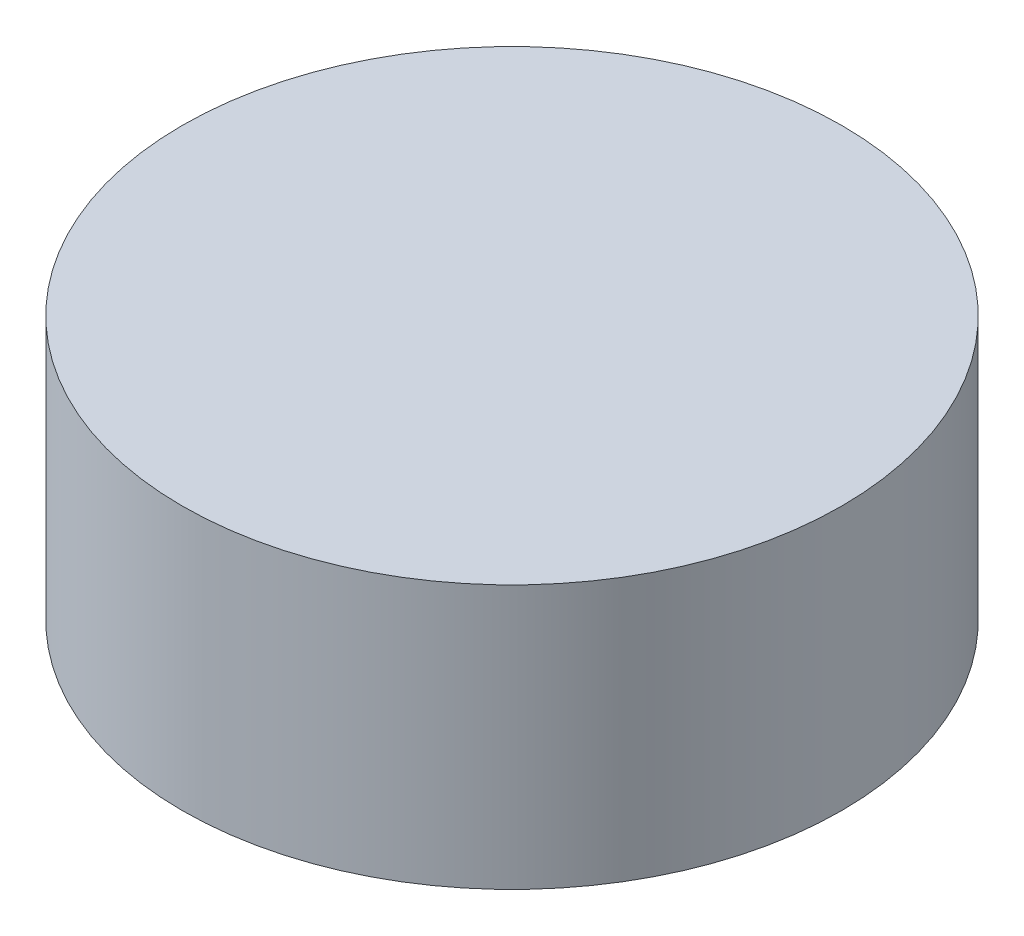
SolidWorks part; units mm, degrees
material "1060 Alloy"
ref_plane "Front Plane" through (0, 0, 0) normal (0, 0, 1) x (1, 0, 0)
ref_plane "Top Plane" through (0, 0, 0) normal (0, 1, 0) x (1, 0, 0)
ref_plane "Right Plane" through (0, 0, 0) normal (1, 0, 0) x (0, 0, -1)
sketch "Sketch1" plane through (0, 0, 0) normal (0, 1, 0) x (1, 0, 0)
  circle A0 centre (0, 0) radius 25
extrude "Boss-Extrude1" add sketch "Sketch1" along normal blind 20
